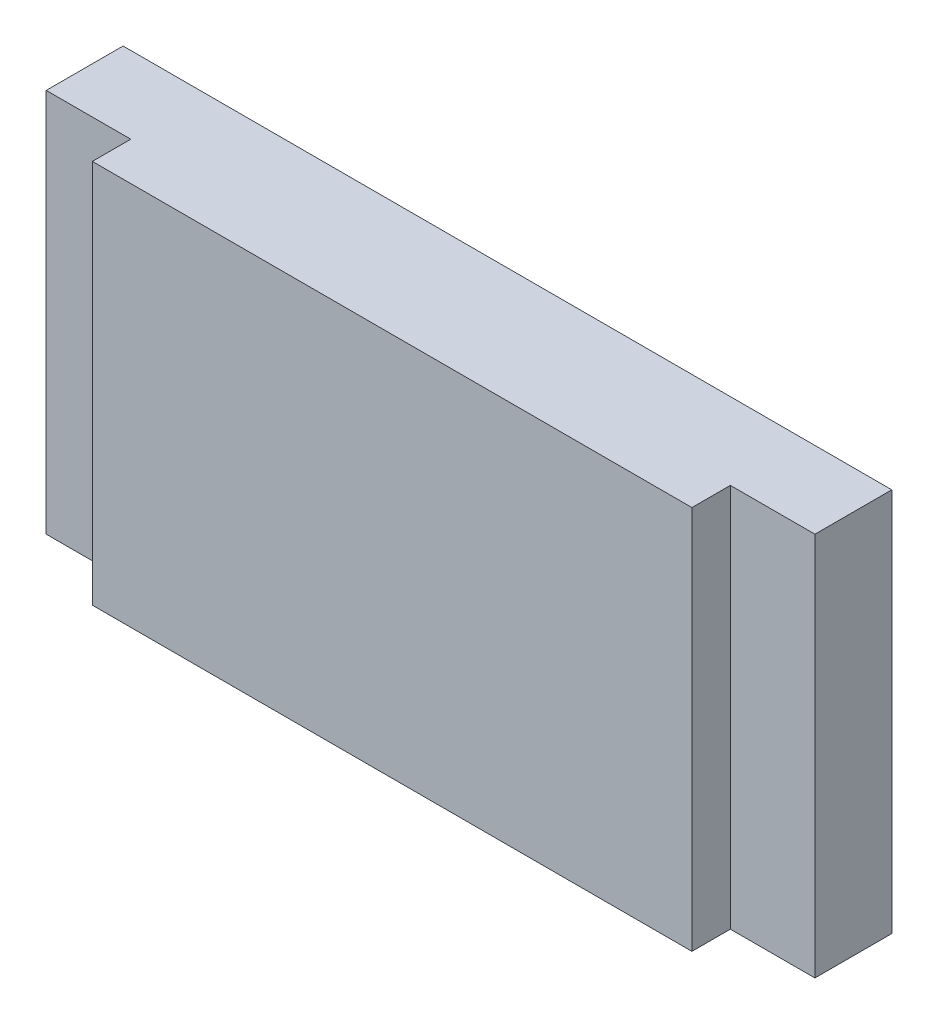
SolidWorks part; units mm, degrees
ref_plane "Front Plane" through (0, 0, 0) normal (0, 0, 1) x (1, 0, 0)
ref_plane "Top Plane" through (0, 0, 0) normal (0, 1, 0) x (1, 0, 0)
ref_plane "Right Plane" through (0, 0, 0) normal (1, 0, 0) x (0, 0, -1)
sketch "Sketch1" plane through (0, 0, 0) normal (0, 1, 0) x (1, 0, 0)
  line L0 (-66.0871, 10.5017) -> (33.9129, 10.5017)
  line L1 (33.9129, 10.5017) -> (33.9129, 0.5017)
  line L2 (33.9129, 0.5017) -> (22.9129, 0.5017)
  line L3 (22.9129, 0.5017) -> (22.9129, -4.4983)
  line L4 (22.9129, -4.4983) -> (-55.0871, -4.4983)
  line L5 (-55.0871, -4.4983) -> (-55.0871, 0.5017)
  line L6 (-55.0871, 0.5017) -> (-66.0871, 0.5017)
  line L7 (-66.0871, 0.5017) -> (-66.0871, 10.5017)
  dimension "D1" = 11
  dimension "D2" = 100
  dimension "D3" = 11
  dimension "D5" = 10
  dimension "D6" = 10
  dimension "D7" = 5
  dimension "D8" = 5
extrude "Boss-Extrude1" add sketch "Sketch1" along normal blind 50
